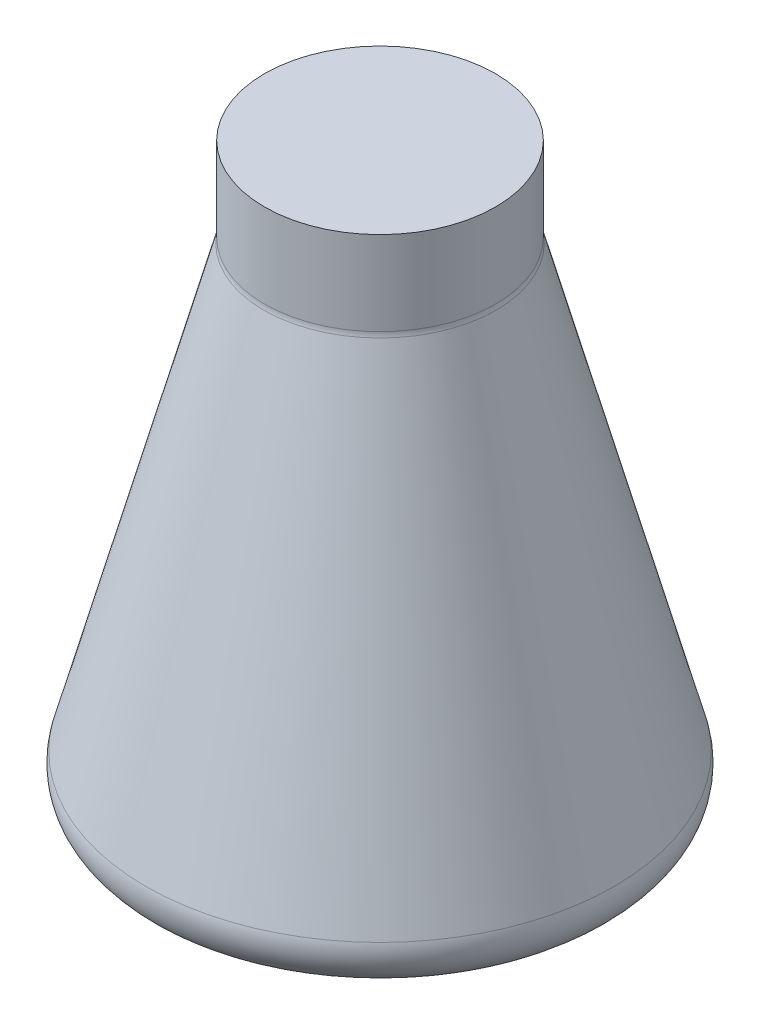
SolidWorks part; units mm, degrees
ref_plane "Front Plane" through (0, 0, 0) normal (0, 0, 1) x (1, 0, 0)
ref_plane "Top Plane" through (0, 0, 0) normal (0, 1, 0) x (1, 0, 0)
ref_plane "Right Plane" through (0, 0, 0) normal (1, 0, 0) x (0, 0, -1)
sketch "Sketch2" plane through (0, 0, 0) normal (0, 0, 1) x (1, 0, 0)
  line L0 (-0.2254, 53.3866) -> (-60.2254, 53.3866)
  line L1 (-0.2254, 53.3866) -> (-0.2254, -246.6134)
  line L2 (-60.2254, 53.3866) -> (-60.2254, 9.7047)
  line L3 (-60.5669, 7.1136) -> (-128.6357, -246.6134)
  line L4 (-128.6357, -246.6134) -> (-0.2254, -246.6134)
  arc A0 (-60.5669, 7.1136) -> (-60.2254, 9.7047) centre (-70.2254, 9.7047) ccw
  point P7 (-60.2254, 8.3866)
  dimension "D1" = 60
  dimension "D4" = 10
  dimension "D2" = 300
  dimension "D3" = 45
revolve "Revolve3" add sketch "Sketch2" angle 360 about L1
fillet "Fillet3" radius 20 1 edges at (-128.6357, -246.6134, 0)
